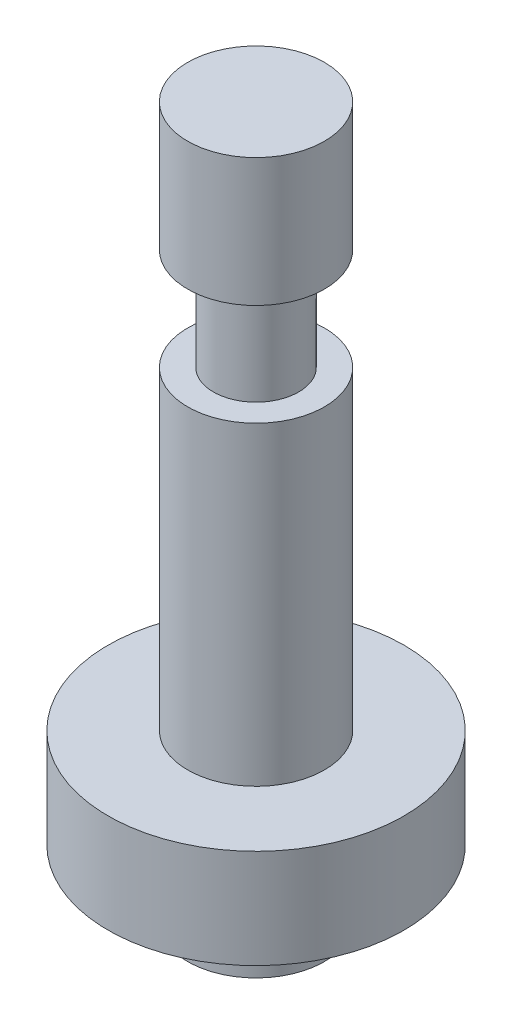
SolidWorks part; units mm, degrees
ref_plane "Alzado" through (0, 0, 0) normal (0, 0, 1) x (1, 0, 0)
ref_plane "Planta" through (0, 0, 0) normal (0, 1, 0) x (1, 0, 0)
ref_plane "Vista lateral" through (0, 0, 0) normal (1, 0, 0) x (0, 0, -1)
sketch "Croquis2" plane through (0, 0, 0) normal (1, 0, 0) x (0, 0, -1)
  line L0 (0, 65.9722) -> (6.35, 65.9722)
  line L1 (6.35, 65.9722) -> (6.35, 54.0756)
  line L2 (6.35, 54.0756) -> (3.9595, 54.0756)
  line L3 (3.9595, 54.0756) -> (3.9595, 44.6123)
  line L4 (3.9595, 44.6123) -> (6.35, 44.6123)
  line L5 (6.35, 44.6123) -> (6.35, 15.4115)
  line L6 (6.35, 15.4115) -> (13.7389, 15.4115)
  line L7 (13.7389, 15.4115) -> (13.7389, 6.2187)
  line L8 (13.7389, 6.2187) -> (6.35, 6.2187)
  line L9 (6.35, 6.2187) -> (6.35, 0)
  line L10 (6.35, 0) -> (0, 0)
  line L11 (0, 0) -> (0, 65.9722)
  point P2 (6.35, 60.0239)
  point P14 (6.35, 3.1093)
  dimension "D1" = 6.35
  dimension ".25" = 6.35
  dimension "D2" = 6.35
revolve "Revolución1" add sketch "Croquis2" angle 360 about L11
